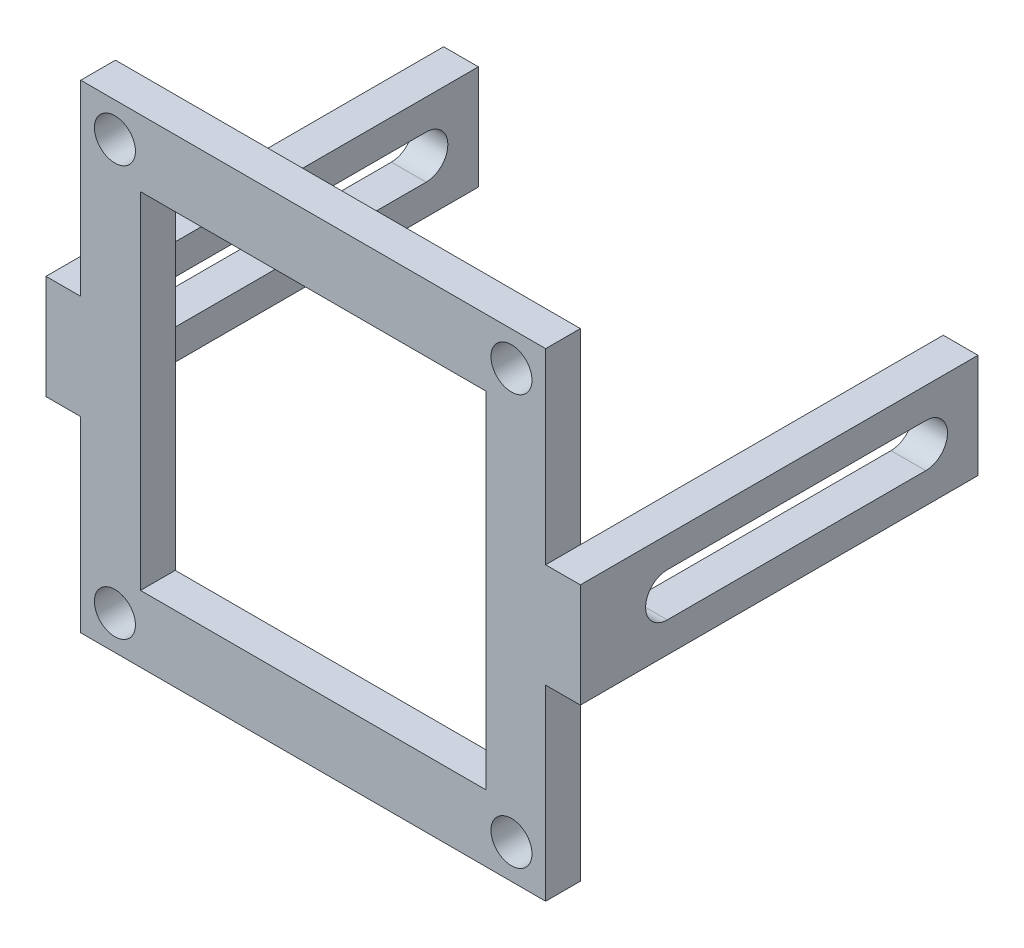
SolidWorks part; units mm, degrees
ref_plane "Front Plane" through (0, 0, 0) normal (0, 0, 1) x (1, 0, 0)
ref_plane "Top Plane" through (0, 0, 0) normal (0, 1, 0) x (1, 0, 0)
ref_plane "Right Plane" through (0, 0, 0) normal (1, 0, 0) x (0, 0, -1)
sketch "Sketch1" plane through (0, 0, 89.7156) normal (0, 0, 1) x (1, 0, 0)
  line L0 (0, 32.8651) -> (0, -2.1349) construction
  line L1 (-17, 32.8651) -> (17, 32.8651)
  line L2 (-17, 32.8651) -> (-17, -2.1349)
  line L3 (-17, -2.1349) -> (17, -2.1349)
  line L4 (17, 32.8651) -> (17, -2.1349)
  line L5 (-12.627, 2.7381) -> (12.627, 2.7381)
  line L6 (-12.627, 2.7381) -> (-12.627, 27.9921)
  line L7 (-12.627, 27.9921) -> (12.627, 27.9921)
  line L8 (12.627, 2.7381) -> (12.627, 27.9921)
  line L9 (0, -2.1349) -> (17, 15.3651) construction
  line L10 (17, 15.3651) -> (-17, 15.3651) construction
  line L11 (0, 27.9921) -> (0, 2.7381) construction
  line L12 (0, 2.7381) -> (12.627, 15.3651) construction
  line L13 (12.627, 15.3651) -> (-12.627, 15.3651) construction
  circle A0 centre (-14.5, 30.3651) radius 1.5
  circle A1 centre (14.5, 30.3651) radius 1.5
  circle A2 centre (14.5, 0.3651) radius 1.5
  circle A3 centre (-14.5, 0.3651) radius 1.5
  point P16 (0, 15.3651)
  dimension "D2" = 3
  dimension "D1" = 25.254
extrude "Boss-Extrude1" add sketch "Sketch1" along normal blind 2.54
sketch "Sketch2" plane through (-17, 0, 0) normal (-1, 0, 0) x (0, 0, 1)
  line L0 (92.2556, 15.3651) -> (63.177, 15.3651) construction
  line L1 (92.2556, 32.8651) -> (92.2556, -2.1349) construction
  line L2 (89.7156, 32.8651) -> (89.7156, -2.1349) construction
  line L3 (63.177, 11.5551) -> (89.7156, 11.5551)
  line L4 (63.177, 11.5551) -> (63.177, 19.1751)
  line L5 (63.177, 19.1751) -> (89.7156, 19.1751)
  line L7 (63.177, 11.5551) -> (89.7156, 19.1751) construction
  line L8 (63.177, 19.1751) -> (89.7156, 11.5551) construction
  line L9 (66.9966, 15.3651) -> (85.896, 15.3651) construction
  line L10 (89.7156, 11.5551) -> (92.2556, 11.5551)
  line L12 (89.7156, 19.1751) -> (92.2556, 19.1751)
  line L13 (92.2556, 11.5551) -> (92.2556, 19.1751)
  line L14 (66.9966, 16.9526) -> (85.896, 16.9526)
  line L15 (66.9966, 13.7776) -> (85.896, 13.7776)
  arc A1 (66.9966, 16.9526) -> (66.9966, 13.7776) centre (66.9966, 15.3651) ccw
  arc A2 (85.896, 13.7776) -> (85.896, 16.9526) centre (85.896, 15.3651) ccw
  point P4 (76.4463, 15.3651)
  point P15 (76.4463, 15.3651)
  point P20 (85.896, 15.3651)
  dimension "D1" = 7.62
  dimension "D2" = 3.175
  dimension "D4" = 18.8994
extrude "Boss-Extrude2" add sketch "Sketch2" along normal blind 2.54
mirror "Mirror1" about plane through (0, 0, 0) normal (1, 0, 0) of "Boss-Extrude2"
